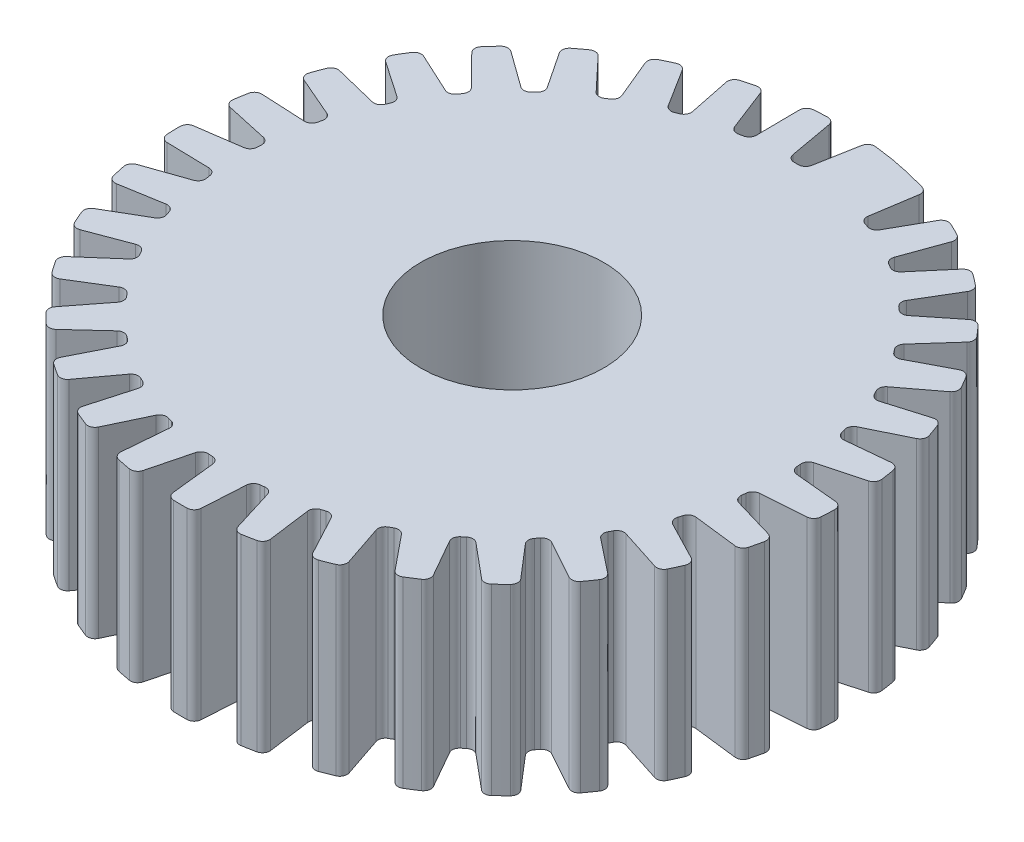
SolidWorks part; units mm, degrees
ref_plane "Front Plane" through (0, 0, 0) normal (0, 0, 1) x (1, 0, 0)
ref_plane "Top Plane" through (0, 0, 0) normal (0, 1, 0) x (1, 0, 0)
ref_plane "Right Plane" through (0, 0, 0) normal (1, 0, 0) x (0, 0, -1)
sketch "Sketch1" plane through (0, 0, 0) normal (0, 1, 0) x (1, 0, 0)
  circle A0 centre (-0.5801, 0.371) radius 18
  dimension "D1" = 36
extrude "Boss-Extrude1" add sketch "Sketch1" along normal blind 10
sketch "Sketch2" plane through (0, 10, 0) normal (0, 1, 0) x (1, 0, 0)
  line L0 (-1, 18.3661) -> (-0.45, 15.3015)
  line L1 (-0.45, 15.3015) -> (0.45, 15.3015)
  line L2 (0.45, 15.3015) -> (1, 18.3015)
  line L3 (1, 18.3015) -> (1, 19.6496)
  line L4 (1, 19.6496) -> (-1, 19.6496)
  line L5 (-1, 19.6496) -> (-1, 18.3661)
  line L6 (0, 0) -> (0, 51.6508) construction
  circle A0 centre (-0.5801, 0.371) radius 18 construction
  point P10 (0, 0)
  point P11 (0, 0)
  dimension "D1" = 3
  dimension "D2" = 0.9
  dimension "D3" = 2
  dimension "D4" = 0.55
  dimension "D5" = 0.45
extrude "Cut-Extrude1" cut sketch "Sketch2" against normal through all
fillet "Fillet1" radius 0.4 4 edges at (0.45, 5, -15.3015) (-0.45, 5, -15.3015) (-1, 5, -18.3661) (1, 5, -18.3015)
pattern_circular "CirPattern1" count 32 every 11 about axis through (-0.5801, 0, -0.371) along (0, 1, 0) of "Cut-Extrude1", "Fillet1"
sketch "Sketch3" plane through (0, 0, 0) normal (0, 1, 0) x (1, 0, 0)
  circle A0 centre (-0.5801, 0.371) radius 5
extrude "Cut-Extrude4" cut sketch "Sketch3" along a picked direction on the side of the normal blind 10
